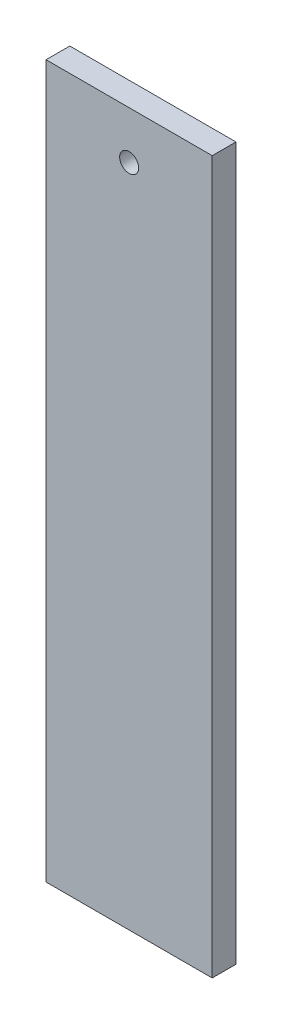
SolidWorks part; units mm, degrees
ref_plane "Front Plane" through (0, 0, 0) normal (0, 0, 1) x (1, 0, 0)
ref_plane "Top Plane" through (0, 0, 0) normal (0, 1, 0) x (1, 0, 0)
ref_plane "Right Plane" through (0, 0, 0) normal (1, 0, 0) x (0, 0, -1)
sketch "Sketch1" plane through (0, 0, 0) normal (0, 0, 1) x (1, 0, 0)
  line L1 (0, 0) -> (35, 0)
  line L2 (0, 0) -> (0, 150)
  line L3 (0, 150) -> (35, 150)
  line L4 (35, 0) -> (35, 150)
  dimension "D1" = 150
  dimension "D2" = 35
extrude "Boss-Extrude1" add sketch "Sketch1" along normal blind 5
sketch "Sketch2" plane through (0, 0, 5) normal (0, 0, 1) x (1, 0, 0)
  line L0 (17.5, 150) -> (17.5, 0) construction
  line L1 (35, 150) -> (0, 150) construction
  line L2 (0, 0) -> (35, 0) construction
  circle A0 centre (17.5, 140) radius 2
  dimension "D1" = 4
  dimension "D2" = 10
extrude "Cut-Extrude1" cut sketch "Sketch2" against normal through all
